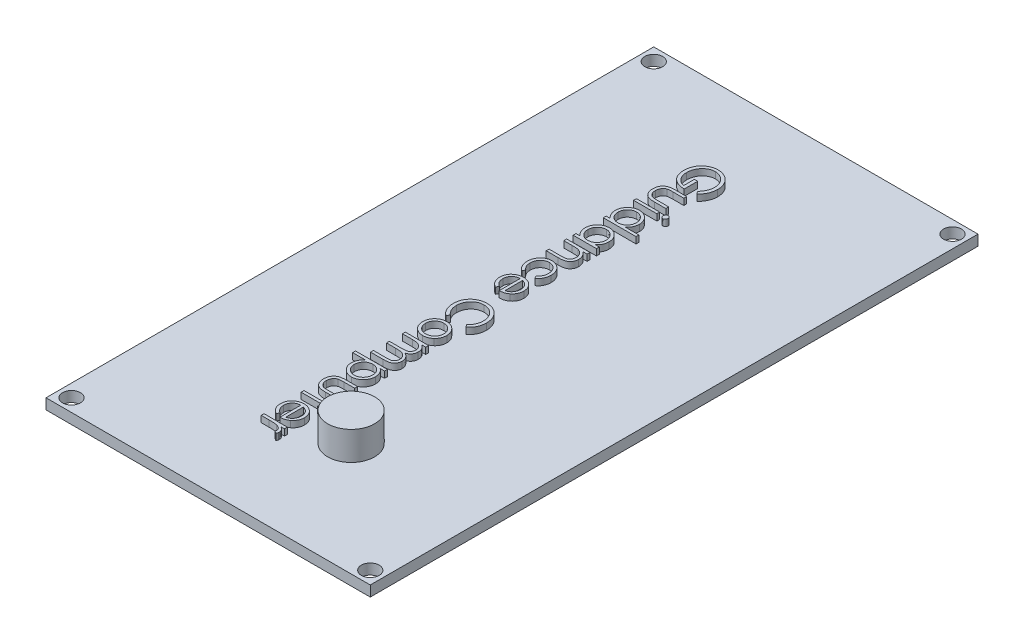
SolidWorks part; units mm, degrees
ref_plane "Front Plane" through (0, 0, 0) normal (0, 0, 1) x (1, 0, 0)
ref_plane "Top Plane" through (0, 0, 0) normal (0, 1, 0) x (1, 0, 0)
ref_plane "Right Plane" through (0, 0, 0) normal (1, 0, 0) x (0, 0, -1)
sketch "Sketch1" plane through (0, 0, 0) normal (0, 1, 0) x (1, 0, 0)
  line L1 (-25.45, -47.7) -> (25.45, -47.7)
  line L2 (-25.45, -47.7) -> (-25.45, 47.7)
  line L3 (-25.45, 47.7) -> (25.45, 47.7)
  line L4 (25.45, -47.7) -> (25.45, 47.7)
  line L5 (-25.45, -47.7) -> (25.45, 47.7) construction
  line L6 (-25.45, 47.7) -> (25.45, -47.7) construction
  point P0 (0, 0)
  dimension "D1" = 50.9
  dimension "D2" = 95.4
extrude "Boss-Extrude1" add sketch "Sketch1" along normal blind 1.65
sketch "Sketch2" plane through (0, 1.65, 0) normal (0, 1, 0) x (1, 0, 0)
  line L0 (-25.45, 45.7) -> (-23.45, 45.7) construction
  line L1 (-25.45, 47.7) -> (-25.45, -47.7) construction
  line L2 (-23.45, 45.7) -> (-23.45, 47.7) construction
  line L3 (25.45, 47.7) -> (-25.45, 47.7) construction
  line L4 (0, 47.7) -> (0, 43.165) construction
  line L5 (25.45, 0) -> (20.0399, 0) construction
  line L6 (25.45, -47.7) -> (25.45, 47.7) construction
  circle A0 centre (-23.45, 45.7) radius 1.4
  circle A1 centre (23.45, 45.7) radius 1.4
  circle A2 centre (23.45, -45.7) radius 1.4
  circle A3 centre (-23.45, -45.7) radius 1.4
  dimension "D2" = 2.8
  dimension "D1" = 2
extrude "Cut-Extrude1" cut sketch "Sketch2" against normal through all
sketch "Sketch3" plane through (0, 1.65, 0) normal (0, 1, 0) x (1, 0, 0)
  line L0 (-5.1759, 38.3707) -> (-5.1759, -38.3707) construction
  line L1 (0, 0) -> (-5.1759, 0) construction
  text T0 "Guidance Computer" font "Century Gothic" height 5
  point P4 (0, 0)
extrude "Boss-Extrude2" add sketch "Sketch3" along normal blind 1
sketch "Sketch4" plane through (0, 1.65, 0) normal (0, 1, 0) x (1, 0, 0)
  line L0 (-25.45, 38.6477) -> (4.7, 38.6477) construction
  line L1 (-25.45, 47.7) -> (-25.45, -47.7) construction
  line L2 (4.7, 38.6477) -> (4.7, -29.95) construction
  line L4 (25.45, -47.7) -> (25.45, 47.7) construction
  line L5 (-25.45, -47.7) -> (25.45, -47.7) construction
  circle A0 centre (4.7, -29.95) radius 3.6787
  dimension "D1" = 20.75
  dimension "D2" = 17.75
extrude "Boss-Extrude3" add sketch "Sketch4" along normal blind 4.5
